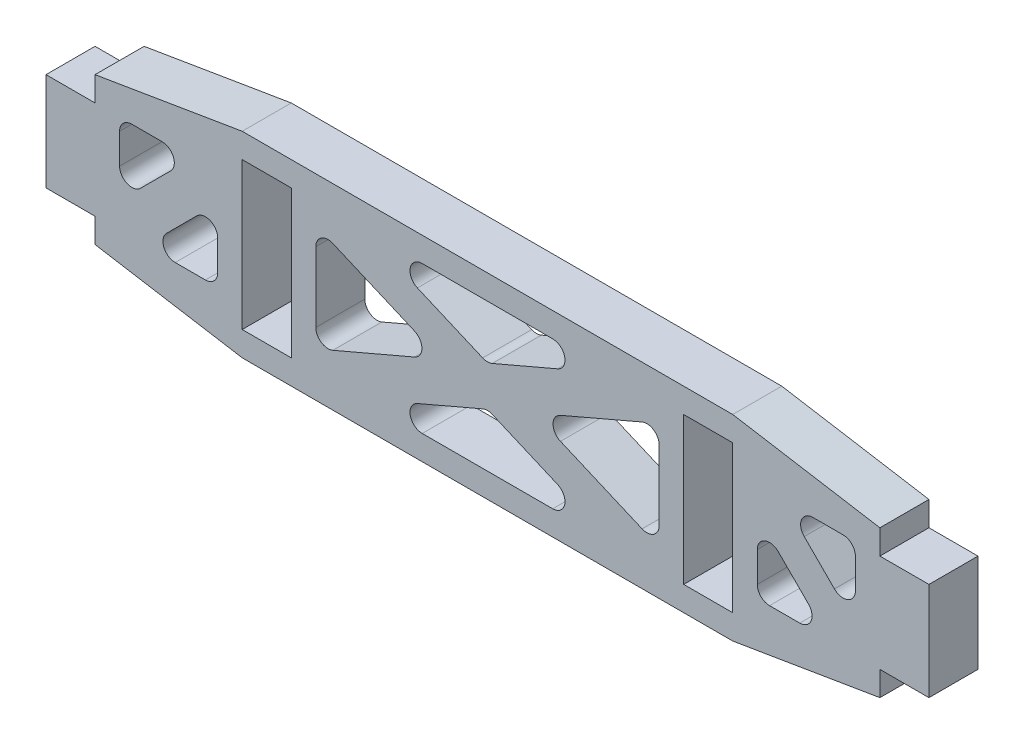
SolidWorks part; units mm, degrees
material "PE High Density"
ref_plane "Front Plane" through (0, 0, 0) normal (0, 0, 1) x (1, 0, 0)
ref_plane "Top Plane" through (0, 0, 0) normal (0, 1, 0) x (1, 0, 0)
ref_plane "Right Plane" through (0, 0, 0) normal (1, 0, 0) x (0, 0, -1)
sketch "Sketch1" plane through (0, 0, 0) normal (0, 0, 1) x (1, 0, 0)
  line L0 (-50.8, -6.35) -> (-50.8, 6.35) construction
  line L1 (-50.8, -9.525) -> (50.8, -9.525) construction
  line L2 (-50.8, -9.525) -> (-50.8, -6.35)
  line L3 (-50.8, 9.525) -> (50.8, 9.525) construction
  line L4 (50.8, -9.525) -> (50.8, -6.35)
  line L5 (-50.8, -9.525) -> (50.8, 9.525) construction
  line L6 (-50.8, 9.525) -> (50.8, -9.525) construction
  line L7 (-50.8, 6.35) -> (-57.15, 6.35)
  line L8 (-50.8, 6.35) -> (-50.8, -6.35) construction
  line L9 (-50.8, -6.35) -> (-57.15, -6.35)
  line L10 (-57.15, 6.35) -> (-57.15, -6.35)
  line L11 (50.8, 6.35) -> (57.15, 6.35)
  line L12 (50.8, 6.35) -> (50.8, -6.35) construction
  line L13 (50.8, -6.35) -> (57.15, -6.35)
  line L14 (57.15, 6.35) -> (57.15, -6.35)
  line L15 (-50.8, 6.35) -> (-50.8, 9.525)
  line L16 (50.8, -6.35) -> (50.8, 6.35) construction
  line L17 (50.8, 6.35) -> (50.8, 9.525)
  line L18 (0, -3.4925) -> (0, 3.4925) construction
  line L19 (-31.75, 9.525) -> (-25.4, 9.525)
  line L20 (-31.75, 9.525) -> (-31.75, -9.525)
  line L21 (-31.75, -9.525) -> (-25.4, -9.525)
  line L22 (-25.4, 9.525) -> (-25.4, -9.525)
  line L23 (31.75, -9.525) -> (25.4, -9.525)
  line L24 (25.4, 9.525) -> (25.4, -9.525)
  line L25 (31.75, 9.525) -> (25.4, 9.525)
  line L26 (31.75, 9.525) -> (31.75, -9.525)
  line L27 (-50.8, 9.525) -> (-31.75, 12.7)
  line L28 (-31.75, 12.7) -> (31.75, 12.7)
  line L29 (31.75, 12.7) -> (50.8, 9.525)
  line L30 (50.8, -9.525) -> (31.75, -12.7)
  line L31 (31.75, -12.7) -> (-31.75, -12.7)
  line L32 (-31.75, -12.7) -> (-50.8, -9.525)
  point P0 (0, 0)
  point P15 (57.15, 0)
  point P16 (-57.15, 0)
  point P26 (-31.75, 0)
  dimension "D1" = 101.6
  dimension "D2" = 6.35
  dimension "D3" = 12.7
  dimension "D4" = 3.175
  dimension "D5" = 50.8
  dimension "D6" = 19.05
  dimension "D7" = 3.175
extrude "Boss-Extrude1" add sketch "Sketch1" along normal mid plane 6.35
sketch "Sketch2" plane through (0, 0, 3.175) normal (0, 0, 1) x (1, 0, 0)
  line L0 (-1000, 0) -> (49000, 0) construction
  line L1 (-47.625, 6.35) -> (-47.625, -6.35)
  line L2 (-47.625, -6.35) -> (-34.925, -6.35)
  line L3 (-34.925, -6.35) -> (-34.925, 6.35)
  line L4 (-34.925, 6.35) -> (-47.625, 6.35)
  line L5 (-50.8, 6.35) -> (-57.15, 6.35) construction
  line L6 (-50.8, 9.525) -> (-50.8, 6.35) construction
  line L7 (-38.2926, 6.35) -> (-47.625, -2.9824)
  line L8 (-50.8, 6.35) -> (-47.625, 6.35) construction
  line L9 (22.225, -9.525) -> (-22.225, -9.525)
  line L10 (22.225, -9.525) -> (22.225, 9.525)
  line L11 (22.225, 9.525) -> (-22.225, 9.525)
  line L12 (-22.225, -9.525) -> (-22.225, 9.525)
  line L13 (22.225, -9.525) -> (-22.225, 9.525) construction
  line L14 (22.225, 9.525) -> (-22.225, -9.525) construction
  line L15 (-34.925, 6.35) -> (-31.75, 6.35) construction
  line L16 (-25.4, 9.525) -> (-22.225, 9.525) construction
  line L17 (22.225, 9.525) -> (25.4, 9.525) construction
  line L18 (-47.625, 6.35) -> (-34.925, -6.35) construction
  line L19 (-34.925, 6.35) -> (-47.625, -6.35) construction
  line L20 (-34.925, 2.9824) -> (-44.2574, -6.35)
  line L21 (-36.6088, 8.0338) -> (-49.3088, -4.6662) construction
  line L22 (-33.2412, 4.6662) -> (-45.9412, -8.0338) construction
  line L23 (22.225, -6.9343) -> (-16.18, 9.525)
  line L24 (16.18, 9.525) -> (-22.225, -6.9343)
  line L25 (16.18, -9.525) -> (-22.225, 6.9343)
  line L26 (22.225, 6.9343) -> (-16.18, -9.525)
  line L27 (23.163, -7.3363) -> (-21.287, 11.7137) construction
  line L28 (21.287, -11.7137) -> (-23.163, 7.3363) construction
  line L29 (21.287, 11.7137) -> (-23.163, -7.3363) construction
  line L30 (23.163, 7.3363) -> (-21.287, -11.7137) construction
  line L31 (0, -3.4925) -> (0, 3.4925) construction
  line L32 (38.2926, 6.35) -> (47.625, -2.9824)
  line L33 (34.925, 2.9824) -> (44.2574, -6.35)
  line L34 (34.925, -6.35) -> (34.925, 6.35)
  line L35 (47.625, -6.35) -> (34.925, -6.35)
  line L36 (47.625, 6.35) -> (47.625, -6.35)
  line L37 (34.925, 6.35) -> (47.625, 6.35)
  line L38 (-25.4, -9.525) -> (-25.4, 9.525) construction
  line L39 (-31.75, 9.525) -> (-31.75, -9.525) construction
  point P9 (-47.625, 0)
  point P14 (0, 0)
  dimension "D1" = 3.175
  dimension "D6" = 19.05
  dimension "D2" = 2.3813
  dimension "D3" = 2.3813
  dimension "D4" = 2.3813
  dimension "D5" = 2.3813
extrude "Cut-Extrude1" cut sketch "Sketch2" against normal through all contours L7 L4 L1 | L3 L20 L2 | L24 L25 L12 | L24 L11 L23 | L10 L26 L23 | L25 L26 L9 | L35 L33 L34 | L37 L32 L36
fillet "Fillet1" radius 1.5875 24 edges at (47.625, -2.9824, 0) (44.2574, -6.35, 0) (34.925, 2.9824, 0) (38.2926, 6.35, 0) (47.625, 6.35, 0) (34.925, -6.35, 0) (22.225, -6.9343, 0) (22.225, 6.9343, 0) (16.18, 9.525, 0) (-16.18, 9.525, 0) (-16.18, -9.525, 0) (16.18, -9.525, 0) (-22.225, -6.9343, 0) (-22.225, 6.9343, 0) (-34.925, 2.9824, 0) (-44.2574, -6.35, 0) (-38.2926, 6.35, 0) (-47.625, -2.9824, 0) (-47.625, 6.35, 0) (-34.925, -6.35, 0) (0, -2.5907, 0) (6.045, 0, 0) (0, 2.5907, 0) (-6.045, 0, 0)
equation "\"D2@Sketch2\"=\"D3@Sketch2\""
equation "\"D5@Sketch2\"=\"D3@Sketch2\""
equation "\"D4@Sketch2\"=\"D5@Sketch2\""
